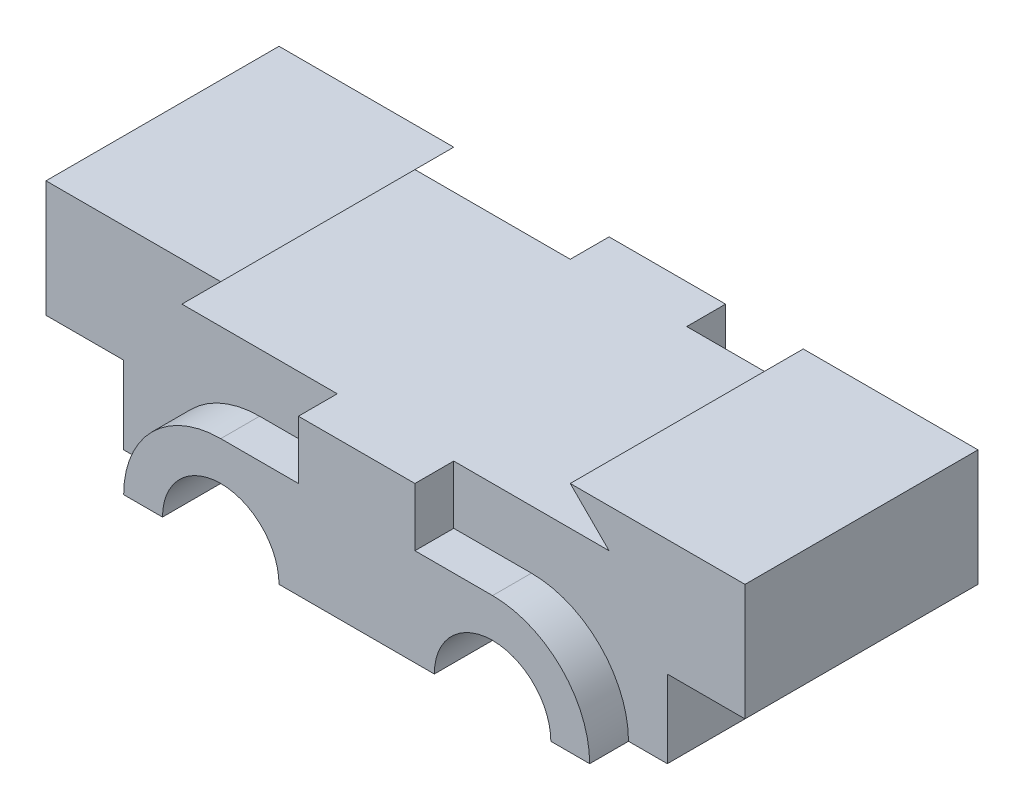
SolidWorks part; units mm, degrees
ref_plane "Front Plane" through (0, 0, 0) normal (0, 0, 1) x (1, 0, 0)
ref_plane "Top Plane" through (0, 0, 0) normal (0, 1, 0) x (1, 0, 0)
ref_plane "Right Plane" through (0, 0, 0) normal (1, 0, 0) x (0, 0, -1)
sketch "Sketch1" plane through (0, 0, 0) normal (0, 0, 1) x (1, 0, 0)
  line L0 (-71.2483, 0) -> (36.2483, 0) construction
  line L1 (-17.5, 13.9851) -> (-17.5, -13.9851) construction
  line L2 (-17.5, 12.5) -> (-7.5, 12.5)
  line L3 (0, 46.3627) -> (0, -16.3766) construction
  line L4 (-7.5, 12.5) -> (-7.5, 20)
  line L5 (-7.5, 20) -> (7.5, 20)
  line L6 (-10, 0) -> (10, 0)
  line L7 (-30, 0) -> (-25, 0)
  line L8 (30, 0) -> (25, 0)
  line L9 (7.5, 12.5) -> (7.5, 20)
  line L10 (17.5, 12.5) -> (7.5, 12.5)
  arc A0 (-25, 0) -> (-10, 0) centre (-17.5, 0) cw
  arc A1 (-30, 0) -> (-17.5, 12.5) centre (-17.5, 0) cw
  arc A2 (30, 0) -> (17.5, 12.5) centre (17.5, 0) ccw
  arc A3 (25, 0) -> (10, 0) centre (17.5, 0) ccw
  point P10 (-17.5, 0)
  point P23 (0, 0)
  point P24 (0, 20)
  dimension "D2" = 7.5
  dimension "D3" = 12.5
  dimension "D1" = 17.5
  dimension "D4" = 7.5
  dimension "D5" = 7.5
extrude "Boss-Extrude1" add sketch "Sketch1" along normal blind 5
sketch "Sketch4" plane through (0, 0, 0) normal (0, 0, -1) x (-1, 0, 0)
  line L0 (0, 31.9604) -> (0, -11.9317) construction
  line L1 (35, 0) -> (-35, 0)
  line L2 (-35, 0) -> (-35, 10)
  line L3 (-35, 10) -> (-45, 10)
  line L4 (-45, 10) -> (-45, 25)
  line L5 (-45, 25) -> (-22.5, 25)
  line L6 (-22.5, 25) -> (-27.5, 20)
  line L7 (-27.5, 20) -> (27.5, 20)
  line L8 (22.5, 25) -> (27.5, 20)
  line L9 (45, 25) -> (22.5, 25)
  line L10 (45, 10) -> (45, 25)
  line L11 (35, 10) -> (45, 10)
  line L12 (35, 0) -> (35, 10)
  arc A0 (-10, 0) -> (-25, 0) centre (-17.5, 0) ccw construction
  point P14 (-17.5, 7.5)
  point P16 (0, 20)
  point P21 (0, 0)
  dimension "D1" = 10
  dimension "D2" = 15
  dimension "D3" = 5
  dimension "D4" = 22.5
  dimension "D5" = 45
  dimension "D6" = 5
  dimension "D7" = 17.5
extrude "Boss-Extrude2" add sketch "Sketch4" along normal blind 15
sketch "Sketch6" plane through (0, 0, 0) normal (0, 0, 1) x (1, 0, 0)
  line L1 (10, 0) -> (25, 0)
  line L2 (10, 0) -> (25, 0)
  line L3 (-25, 0) -> (-10, 0)
  line L4 (-25, 0) -> (-10, 0)
  arc A1 (25, 0) -> (10, 0) centre (17.5, 0) ccw
  arc A2 (25, 0) -> (10, 0) centre (17.5, 0) ccw
  arc A3 (-10, 0) -> (-25, 0) centre (-17.5, 0) ccw
  arc A4 (-10, 0) -> (-25, 0) centre (-17.5, 0) ccw
  dimension "D1" = 0
  dimension "D2" = 0
extrude "Cut-Extrude1" cut sketch "Sketch6" against normal blind 15
sketch "Sketch7" plane through (0, 0, 0) normal (0, 1, 0) x (1, 0, 0)
  line L0 (0, -13.2088) -> (0, 25.7591) construction
  line L1 (-35, 15) -> (-45, 15) construction
  circle A0 centre (0, 0) radius 2.25
  circle A1 centre (-30, 7.5) radius 2.25
  circle A2 centre (30, 7.5) radius 2.25
  dimension "D1" = 4.5
  dimension "D2" = 7.5
  dimension "D3" = 30
extrude "Cut-Extrude2" cut sketch "Sketch7" along normal blind 15
mirror "Mirror2" about plane through (0, 0, -15) normal (0, 0, -1) of bodies 105
